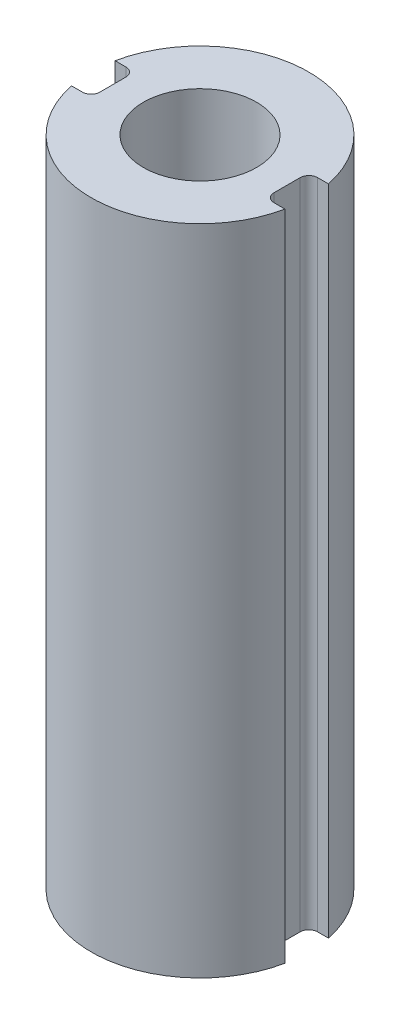
SolidWorks part; units mm, degrees
material "ABS"
ref_plane "Front Plane" through (0, 0, 0) normal (0, 0, 1) x (1, 0, 0)
ref_plane "Top Plane" through (0, 0, 0) normal (0, 1, 0) x (1, 0, 0)
ref_plane "Right Plane" through (0, 0, 0) normal (1, 0, 0) x (0, 0, -1)
sketch "Sketch1" plane through (0, 0, 0) normal (0, 1, 0) x (1, 0, 0)
  line L0 (0, 0) -> (0, 0.5711) construction
  line L1 (2.54, -0.635) -> (3.1109, -0.635)
  line L2 (-2.54, -0.635) -> (-3.1109, -0.635)
  line L3 (-2.54, -0.635) -> (-2.54, 0.635)
  line L4 (-2.54, 0.635) -> (-3.1109, 0.635)
  line L5 (2.54, -0.635) -> (2.54, 0.635)
  line L6 (-2.54, -0.635) -> (-3.175, 0) construction
  line L7 (-2.54, 0.635) -> (-3.175, 0) construction
  line L8 (2.54, 0.635) -> (3.1109, 0.635)
  arc A0 (-3.1109, -0.635) -> (3.1109, -0.635) centre (0, 0) ccw
  arc A1 (3.1109, 0.635) -> (-3.1109, 0.635) centre (0, 0) ccw
  point P3 (-3.175, 0)
  dimension "D1" = 6.35
  dimension "D2" = 1.27
  dimension "D3" = 0.635
extrude "Boss-Extrude1" add sketch "Sketch1" along normal blind 19.05
sketch "Sketch2" plane through (0, 19.05, 0) normal (0, 1, 0) x (1, 0, 0)
  circle A0 centre (0, 0) radius 1.651
  dimension "D1" = 3.302
extrude "Cut-Extrude1" cut sketch "Sketch2" against normal blind 12.7
fillet "Fillet1" radius 0.254 4 edges at (2.54, 9.525, 0.635) (2.54, 9.525, -0.635) (-2.54, 9.525, 0.635) (-2.54, 9.525, -0.635)
